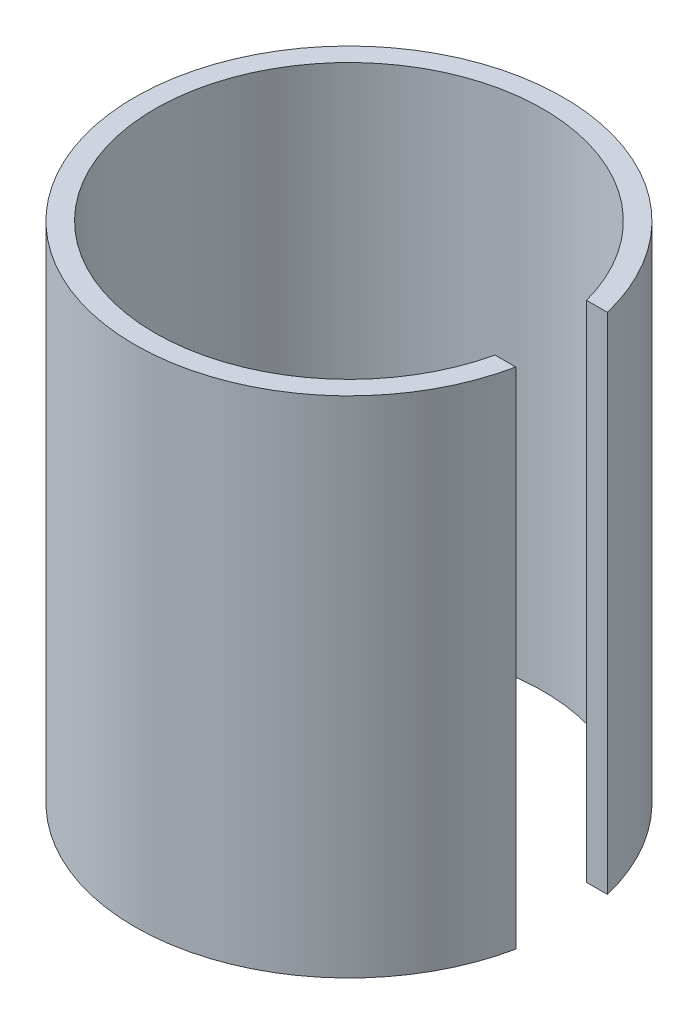
SolidWorks part; units mm, degrees
ref_plane "Plano frontal" through (0, 0, 0) normal (0, 0, 1) x (1, 0, 0)
ref_plane "Plano superior" through (0, 0, 0) normal (0, 1, 0) x (1, 0, 0)
ref_plane "Plano direito" through (0, 0, 0) normal (1, 0, 0) x (0, 0, -1)
sketch "Esboço1" plane through (0, 0, 0) normal (0, 1, 0) x (1, 0, 0)
  line L0 (75.0592, -17.0946) -> (83.2633, -17.0946)
  line L1 (74.3722, 19.8719) -> (82.6445, 19.8719)
  arc A0 (82.6445, 19.8719) -> (83.2633, -17.0946) centre (0, 0) ccw
  arc A1 (74.3722, 19.8719) -> (75.0592, -17.0946) centre (0, 0) ccw
  dimension "D1" = 85
extrude "Ressalto-extrusão1" add sketch "Esboço1" along normal blind 200
